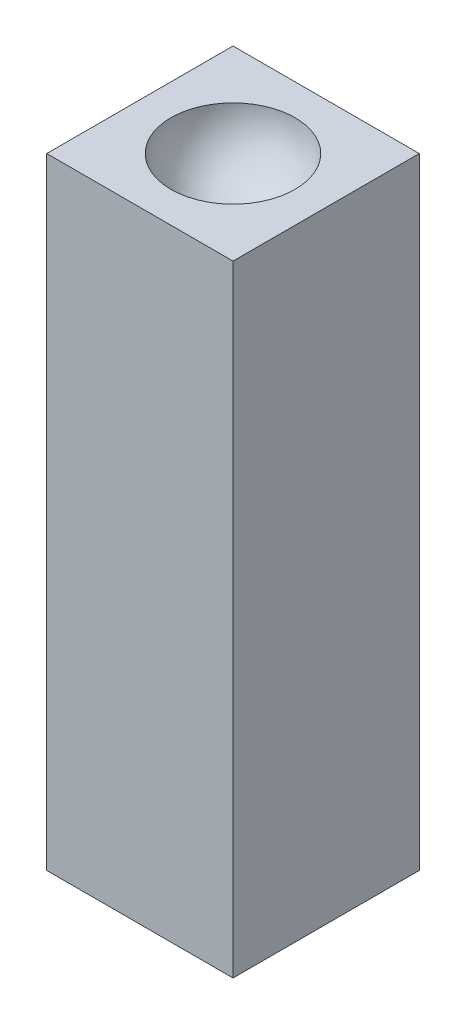
SolidWorks part; units mm, degrees
ref_plane "Front Plane" through (0, 0, 0) normal (0, 0, 1) x (1, 0, 0)
ref_plane "Top Plane" through (0, 0, 0) normal (0, 1, 0) x (1, 0, 0)
ref_plane "Right Plane" through (0, 0, 0) normal (1, 0, 0) x (0, 0, -1)
sketch "Sketch1" plane through (0, 0, 0) normal (0, 1, 0) x (1, 0, 0)
  line L1 (-3, 3) -> (3, 3)
  line L2 (-3, 3) -> (-3, -3)
  line L3 (-3, -3) -> (3, -3)
  line L4 (3, 3) -> (3, -3)
  line L5 (-3, 3) -> (3, -3) construction
  line L6 (-3, -3) -> (3, 3) construction
  point P0 (0, 0)
  point P1 (0, 0)
  dimension "D1" = 6
  dimension "D2" = 6
extrude "Boss-Extrude1" add sketch "Sketch1" along normal blind 20
sketch "Sketch3" plane through (0, 20, 0) normal (0, 1, 0) x (1, 0, 0)
  line L0 (-2, 0) -> (2, 0)
  arc A0 (2, 0) -> (-2, 0) centre (0, 0) ccw
  dimension "D1" = 4
revolve "Cut-Revolve1" cut sketch "Sketch3" angle 360 about L0
